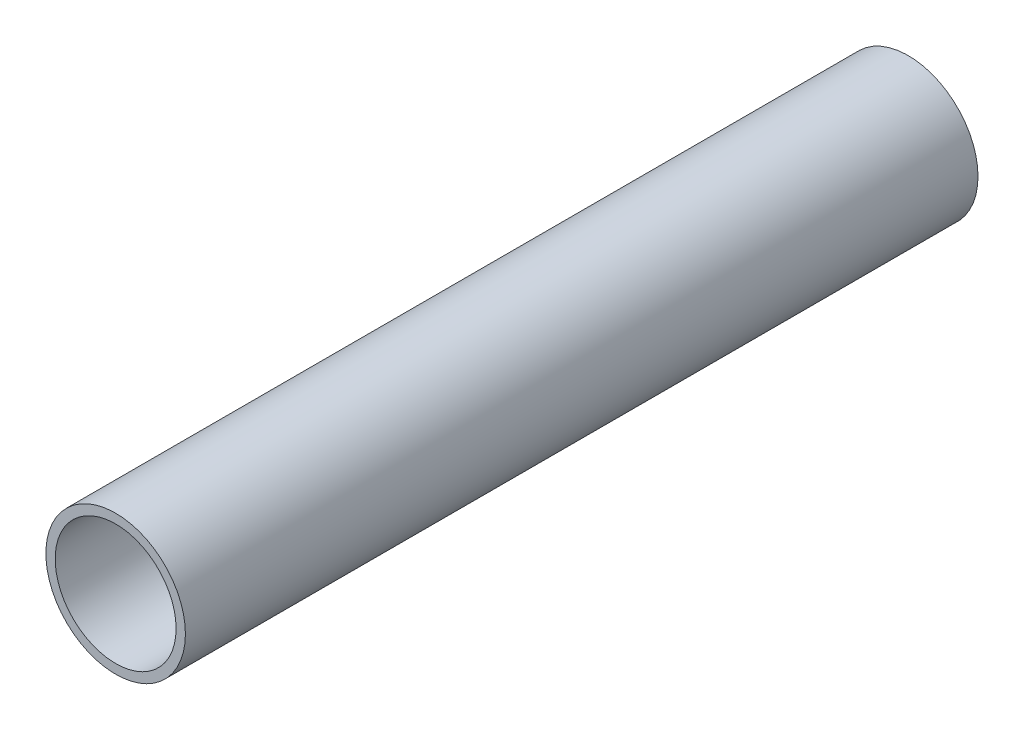
SolidWorks part; units mm, degrees
ref_plane "Front Plane" through (0, 0, 0) normal (0, 0, 1) x (1, 0, 0)
ref_plane "Top Plane" through (0, 0, 0) normal (0, 1, 0) x (1, 0, 0)
ref_plane "Right Plane" through (0, 0, 0) normal (1, 0, 0) x (0, 0, -1)
sketch "Sketch1" plane through (0, 0, 0) normal (0, 0, 1) x (1, 0, 0)
  circle A0 centre (0, 0) radius 9.525
  circle A1 centre (0, 0) radius 8.255
  dimension "D1" = 16.51
  dimension "D2" = 19.05
extrude "Boss-Extrude1" add sketch "Sketch1" along normal blind 108.204
